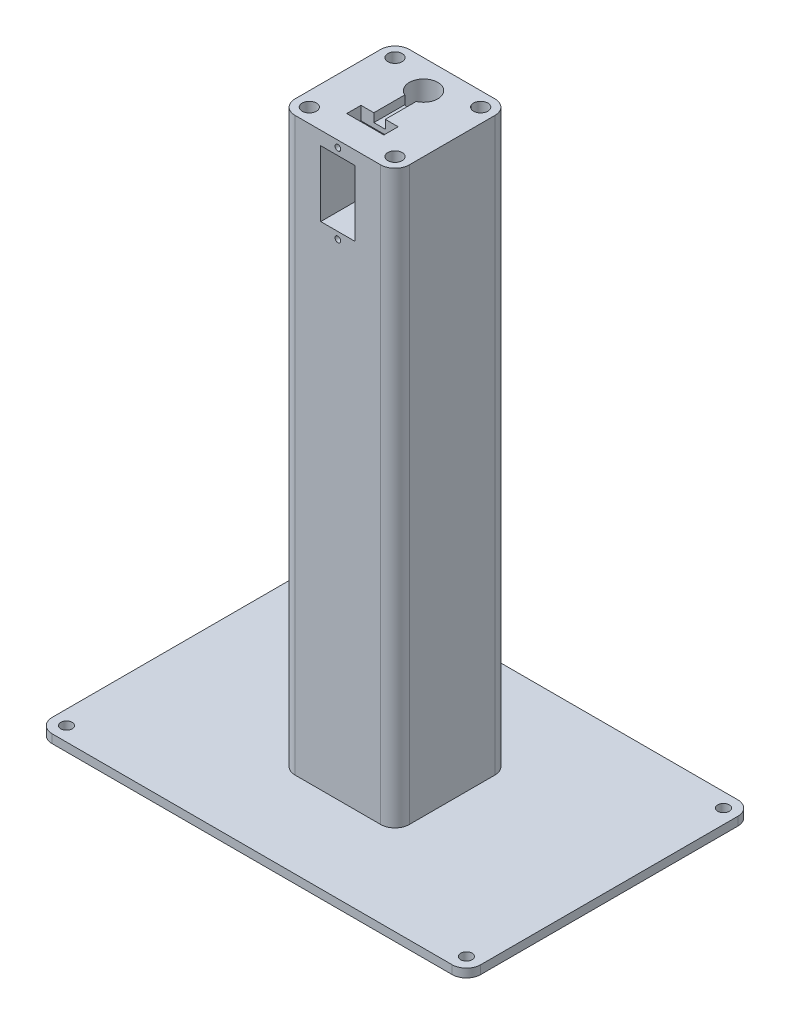
SolidWorks part; units mm, degrees
ref_plane "Front Plane" through (0, 0, 0) normal (0, 0, 1) x (1, 0, 0)
ref_plane "Top Plane" through (0, 0, 0) normal (0, 1, 0) x (1, 0, 0)
ref_plane "Right Plane" through (0, 0, 0) normal (1, 0, 0) x (0, 0, -1)
sketch "Sketch1" plane through (0, 0, 0) normal (0, 1, 0) x (1, 0, 0)
  line L1 (0, 0) -> (40, 0)
  line L2 (0, 0) -> (0, 40)
  line L3 (0, 40) -> (40, 40)
  line L4 (40, 0) -> (40, 40)
  dimension "D1" = 40
  dimension "D2" = 40
extrude "Boss-Extrude1" add sketch "Sketch1" along normal blind 200
sketch "Sketch2" plane through (0, 0, 0) normal (0, 0, 1) x (1, 0, 0)
  line L0 (0, 200) -> (0, 0) construction
  line L1 (14, 195.3) -> (26, 195.3)
  line L2 (14, 195.3) -> (14, 172.3)
  line L3 (14, 172.3) -> (26, 172.3)
  line L4 (26, 195.3) -> (26, 172.3)
  line L5 (0, 200) -> (40, 200) construction
  dimension "D1" = 23
  dimension "D2" = 12
  dimension "D3" = 14
  dimension "D4" = 4.7
extrude "Cut-Extrude1" cut sketch "Sketch2" against normal blind 15.9
sketch "Sketch3" plane through (0, 0, 0) normal (0, 0, 1) x (1, 0, 0)
  line L0 (0, 200) -> (0, 0) construction
  line L1 (0, 200) -> (40, 200) construction
  line L2 (14, 172.3) -> (26, 172.3) construction
  circle A0 centre (20, 197.7) radius 1
  circle A1 centre (20, 169.9) radius 1
  dimension "D1" = 20
  dimension "D3" = 20
  dimension "D2" = 2.3
  dimension "D4" = 2.4
extrude "Cut-Extrude2" cut sketch "Sketch3" against normal blind 4
sketch "Sketch4" plane through (0, 200, 0) normal (0, 1, 0) x (1, 0, 0)
  line L0 (0, 40) -> (0, 0) construction
  line L2 (40, 40) -> (0, 40) construction
  circle A0 centre (20, 30) radius 5
  dimension "D1" = 20
  dimension "D2" = 10
extrude "Cut-Extrude3" cut sketch "Sketch4" against normal through all
sketch "Sketch5" plane through (0, 200, 0) normal (0, 1, 0) x (1, 0, 0)
  line L0 (0, 40) -> (0, 0) construction
  line L1 (13.5, 14.6) -> (26.5, 14.6)
  line L2 (13.5, 14.6) -> (13.5, 9.6)
  line L3 (13.5, 9.6) -> (26.5, 9.6)
  line L4 (26.5, 14.6) -> (26.5, 9.6)
  line L5 (0, 0) -> (40, 0) construction
  dimension "D1" = 13
  dimension "D2" = 5
  dimension "D3" = 13.5
  dimension "D4" = 9.6
extrude "Cut-Extrude4" cut sketch "Sketch5" against normal blind 4.7
sketch "Sketch6" plane through (0, 200, 0) normal (0, 1, 0) x (1, 0, 0)
  line L0 (26.5, 14.6) -> (13.5, 14.6) construction
  line L1 (18, 25.4174) -> (22, 25.4174)
  line L2 (18, 25.4174) -> (18, 14.6)
  line L3 (18, 14.6) -> (22, 14.6)
  line L4 (22, 25.4174) -> (22, 14.6)
  line L5 (0, 40) -> (0, 0) construction
  circle A0 centre (20, 30) radius 5 construction
  dimension "D1" = 4
  dimension "D2" = 18
extrude "Cut-Extrude5" cut sketch "Sketch6" against normal blind 3
fillet "Fillet1" radius 5 4 edges at (40, 100, 0) (40, 100, -40) (0, 100, -40) (0, 100, 0)
sketch "Sketch7" plane through (0, 0, 0) normal (0, -1, 0) x (1, 0, 0)
  line L0 (0, -35) -> (0, -5) construction
  line L1 (-55, 30) -> (95, 30)
  line L2 (-55, 30) -> (-55, -70)
  line L3 (-55, -70) -> (95, -70)
  line L4 (95, 30) -> (95, -70)
  line L5 (35, -40) -> (5, -40) construction
  dimension "D1" = 55
  dimension "D2" = 30
  dimension "D3" = 100
  dimension "D4" = 150
extrude "Boss-Extrude2" add sketch "Sketch7" along normal blind 3
sketch "Sketch9" plane through (0, -3, 0) normal (0, -1, 0) x (1, 0, 0)
  line L0 (-55, 30) -> (-55, -70) construction
  line L1 (95, 30) -> (-55, 30) construction
  circle A0 centre (20, -30) radius 5
  dimension "D1" = 75
  dimension "D2" = 60
extrude "Cut-Extrude6" cut sketch "Sketch9" against normal blind 3
sketch "Sketch10" plane through (0, 0, 0) normal (0, 1, 0) x (1, 0, 0)
  line L0 (-55, -30) -> (-55, 70) construction
  line L1 (-55, 70) -> (95, 70) construction
  circle A0 centre (-50, 65) radius 2
  dimension "D1" = 5
  dimension "D2" = 5
extrude "Cut-Extrude7" cut sketch "Sketch10" against normal through all
ref_plane "Plane1" through (20, 0, 0) normal (-1, 0, 0) x (0, 0, 1)
mirror "Mirror1" about plane through (20, 0, 0) normal (-1, 0, 0) of "Cut-Extrude7"
ref_plane "Plane2" through (0, 0, -20) normal (0, 0, -1) x (-1, 0, 0)
mirror "Mirror2" about plane through (0, 0, -20) normal (0, 0, -1) of "Mirror1", "Cut-Extrude7"
sketch "Sketch11" plane through (0, 200, 0) normal (0, 1, 0) x (1, 0, 0)
  line L0 (0, 35) -> (0, 5) construction
  circle A0 centre (5, 35) radius 2.5
  dimension "D1" = 5
  dimension "D2" = 5
extrude "Cut-Extrude8" cut sketch "Sketch11" against normal blind 5
mirror "Mirror3" about plane through (0, 0, -20) normal (0, 0, -1) of "Cut-Extrude8"
mirror "Mirror4" about plane through (20, 0, 0) normal (-1, 0, 0) of "Mirror3", "Cut-Extrude8"
fillet "Fillet2" radius 5 4 edges at (-55, -1.5, 30) (-55, -1.5, -70) (95, -1.5, -70) (95, -1.5, 30)
